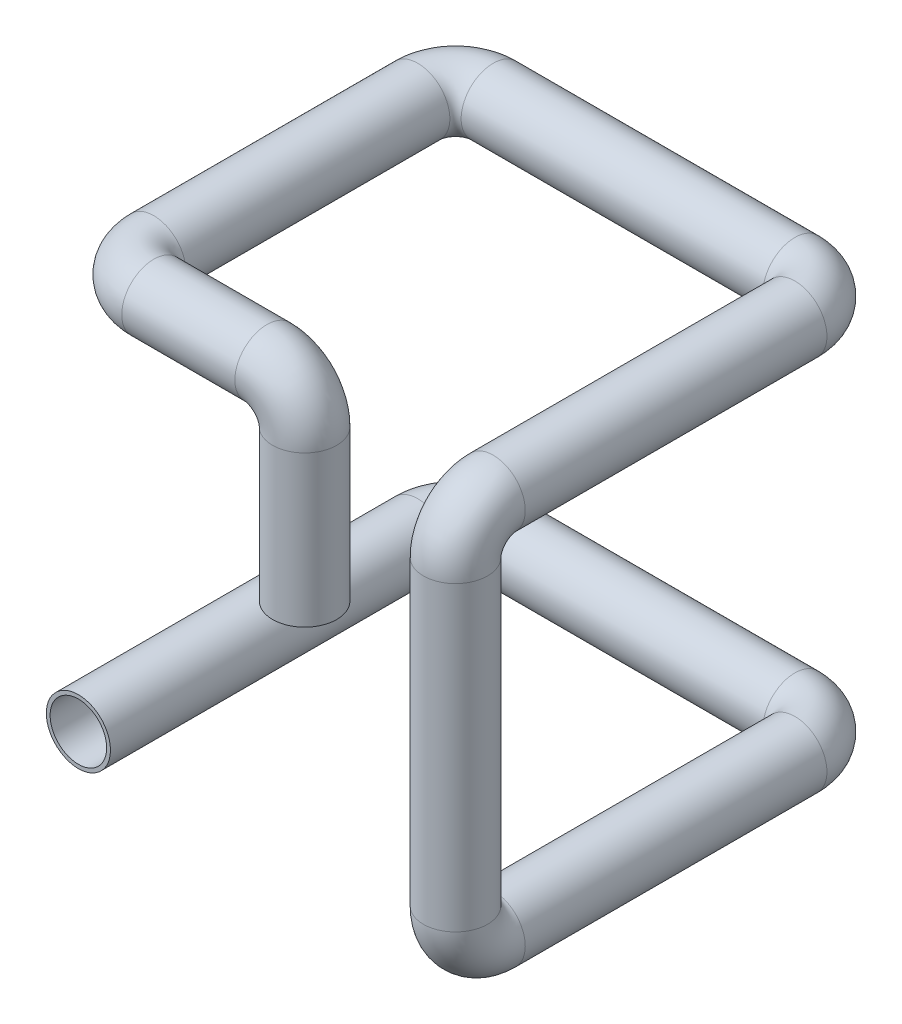
SolidWorks part; units mm, degrees
material "Cast Carbon Steel"
ref_plane "Front Plane" through (0, 0, 0) normal (0, 0, 1) x (1, 0, 0)
ref_plane "Top Plane" through (0, 0, 0) normal (0, 1, 0) x (1, 0, 0)
ref_plane "Right Plane" through (0, 0, 0) normal (1, 0, 0) x (0, 0, -1)
sketch3d "3DSketch2"
  line L0 (0, 0, 0) -> (0, 0, -90)
  line L1 (10, 0, -100) -> (90, 0, -100)
  line L2 (100, 0, -90) -> (100, 0, -10)
  line L3 (100, 10, 0) -> (100, 90, 0)
  line L4 (100, 100, -10) -> (100, 100, -90)
  line L5 (90, 100, -100) -> (10, 100, -100)
  line L6 (0, 100, -90) -> (0, 100, -20)
  line L7 (10, 100, -10) -> (40, 100, -10)
  line L8 (50, 90, -10) -> (50, 50, -10)
  arc A0 (40, 100, -10) -> (50, 90, -10) centre (40, 90, -10) ccw
  arc A1 (0, 100, -20) -> (10, 100, -10) centre (10, 100, -20) ccw
  arc A2 (10, 100, -100) -> (0, 100, -90) centre (10, 100, -90) ccw
  arc A3 (100, 100, -90) -> (90, 100, -100) centre (90, 100, -90) ccw
  arc A4 (100, 90, 0) -> (100, 100, -10) centre (100, 90, -10) ccw
  arc A5 (100, 0, -10) -> (100, 10, 0) centre (100, 10, -10) ccw
  arc A6 (90, 0, -100) -> (100, 0, -90) centre (90, 0, -90) ccw
  arc A7 (0, 0, -90) -> (10, 0, -100) centre (10, 0, -90) ccw
  point P13 (50, 100, -10)
  point P14 (40, 90, -20)
  point P17 (0, 100, -10)
  point P18 (10, 110, -20)
  point P21 (0, 100, -100)
  point P22 (10, 110, -90)
  point P25 (100, 100, -100)
  point P26 (90, 110, -90)
  point P29 (100, 100, 0)
  point P30 (90, 90, -10)
  point P33 (100, 0, 0)
  point P34 (90, 10, -10)
  point P37 (100, 0, -100)
  point P38 (90, -10, -90)
  point P41 (0, 0, -100)
  point P42 (10, -10, -90)
  dimension "D10" = 10
  dimension "D1" = 100
  dimension "D2" = 100
  dimension "D3" = 100
  dimension "D4" = 100
  dimension "D5" = 100
  dimension "D6" = 100
  dimension "D7" = 90
  dimension "D8" = 50
  dimension "D9" = 50
sketch "Sketch1" plane through (0, 0, 0) normal (0, 0, 1) x (1, 0, 0)
  circle A0 centre (0, 0) radius 7.5
  dimension "D1" = 15
sweep "Sweep-Thin1" add profiles "Sketch1" path "3DSketch2" parameters "D1"=1
